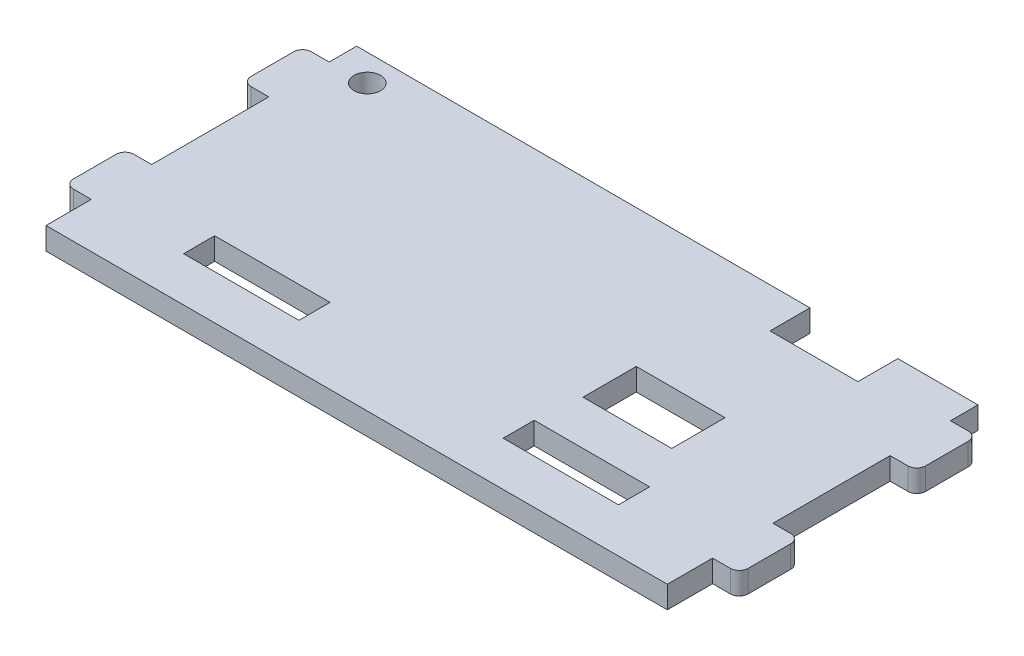
SolidWorks part; units mm, degrees
ref_plane "前视" through (0, 0, 0) normal (0, 0, 1) x (1, 0, 0)
ref_plane "上视" through (0, 0, 0) normal (0, 1, 0) x (1, 0, 0)
ref_plane "右视" through (0, 0, 0) normal (1, 0, 0) x (0, 0, -1)
sketch "草图1" plane through (0, 0, 0) normal (0, 1, 0) x (1, 0, 0)
  line L1 (-38, 17.5) -> (38, 17.5)
  line L2 (-38, 17.5) -> (-38, -17.5)
  line L3 (-38, -17.5) -> (38, -17.5)
  line L4 (38, 17.5) -> (38, -17.5)
  line L5 (-38, 17.5) -> (38, -17.5) construction
  line L6 (-38, -17.5) -> (38, 17.5) construction
  point P0 (0, 0)
  dimension "D1" = 35
  dimension "D2" = 76
extrude "凸台-拉伸1" add sketch "草图1" along normal blind 2.5
sketch "草图2" plane through (0, 2.5, 0) normal (0, 1, 0) x (1, 0, 0)
  line L0 (-38, -17.5) -> (38, -17.5) construction
  line L1 (-24.5, -9) -> (-11.5, -9)
  line L2 (-24.5, -9) -> (-24.5, -12.5)
  line L3 (-24.5, -12.5) -> (-11.5, -12.5)
  line L4 (-11.5, -9) -> (-11.5, -12.5)
  line L5 (-24.5, -9) -> (-11.5, -12.5) construction
  line L6 (-24.5, -12.5) -> (-11.5, -9) construction
  line L7 (-38, 17.5) -> (-38, -17.5) construction
  line L8 (0, 0) -> (0, -2.6782) construction
  line L9 (24.5, -12.5) -> (11.5, -12.5)
  line L10 (11.5, -9) -> (11.5, -12.5)
  line L11 (24.5, -9) -> (11.5, -9)
  line L12 (24.5, -9) -> (24.5, -12.5)
  point P0 (-18, -10.75)
  dimension "D1" = 5
  dimension "D2" = 13.5
  dimension "D3" = 13
  dimension "D4" = 3.5
extrude "切除-拉伸1" cut sketch "草图2" against normal through all
sketch "草图3" plane through (0, 2.5, 0) normal (0, 1, 0) x (1, 0, 0)
  line L0 (-38, -17.5) -> (-35, -17.5)
  line L1 (-38, -17.5) -> (38, -17.5) construction
  line L2 (-35, -17.5) -> (-35, -12.4)
  line L3 (-35, -12.4) -> (-38, -12.4)
  line L4 (-38, 17.5) -> (-38, -17.5) construction
  line L5 (-38, -12.4) -> (-38, -17.5)
  line L6 (-38, 17.5) -> (-35, 17.5)
  line L7 (38, 17.5) -> (-38, 17.5) construction
  line L8 (-35, 17.5) -> (-35, 14.4)
  line L9 (-35, 14.4) -> (-38, 14.4)
  line L10 (-38, 14.4) -> (-38, 17.5)
  line L11 (-38, 7.6) -> (-35, 7.6)
  line L12 (-35, 7.6) -> (-35, -5.6)
  line L13 (-35, -5.6) -> (-38, -5.6)
  line L14 (-38, -5.6) -> (-38, 7.6)
  line L15 (0, 0) -> (0, 5.419) construction
  line L16 (38, -17.5) -> (35, -17.5)
  line L17 (38, -12.4) -> (38, -17.5)
  line L18 (35, -17.5) -> (35, -12.4)
  line L19 (35, -12.4) -> (38, -12.4)
  line L20 (35, -5.6) -> (38, -5.6)
  line L21 (38, -5.6) -> (38, 7.6)
  line L22 (35, 7.6) -> (35, -5.6)
  line L23 (38, 7.6) -> (35, 7.6)
  line L24 (35, 14.4) -> (38, 14.4)
  line L25 (35, 17.5) -> (35, 14.4)
  line L26 (38, 17.5) -> (35, 17.5)
  line L27 (38, 14.4) -> (38, 17.5)
  dimension "D1" = 3
  dimension "D2" = 5.1
  dimension "D3" = 3
  dimension "D4" = 3.1
  dimension "D5" = 3
  dimension "D6" = 6.8
  dimension "D7" = 6.8
extrude "切除-拉伸2" cut sketch "草图3" against normal through all
fillet "圆角1" radius 1 8 edges at (38, 1.25, -14.4) (38, 1.25, -7.6) (38, 1.25, 5.6) (38, 1.25, 12.4) (-38, 1.25, 12.4) (-38, 1.25, 5.6) (-38, 1.25, -7.6) (-38, 1.25, -14.4)
sketch "草图4" plane through (0, 2.5, 0) normal (0, 1, 0) x (1, 0, 0)
  line L0 (35, 17.5) -> (-35, 17.5) construction
  line L1 (35, 17.5) -> (35, 14.4) construction
  line L2 (-35, 14.4) -> (-35, 17.5) construction
  line L3 (18.0812, 14.5) -> (26.9965, 14.5) construction
  line L4 (25.9681, 17.5) -> (25.9681, 13)
  line L5 (25.9681, 13) -> (16.0681, 13)
  line L6 (16.0681, 13) -> (16.0681, 17.5)
  line L7 (16.0681, 17.5) -> (25.9681, 17.5)
  circle A0 centre (-30.8, 14.5) radius 1.5
  point P4 (-35, 15.95)
  dimension "D1" = 3
  dimension "D2" = 4.2
  dimension "D3" = 4.5
  dimension "D4" = 9.9
  dimension "D5" = 9.0319
extrude "切除-拉伸3" cut sketch "草图4" against normal through all
sketch "草图5" plane through (0, 2.5, 0) normal (0, 1, 0) x (1, 0, 0)
  line L0 (35, 7.6) -> (35, -5.6) construction
  line L1 (12, 2) -> (22, 2)
  line L2 (12, 2) -> (12, -4)
  line L3 (12, -4) -> (22, -4)
  line L4 (22, 2) -> (22, -4)
  line L5 (12, 2) -> (22, -4) construction
  line L6 (12, -4) -> (22, 2) construction
  line L7 (24.5, -9) -> (11.5, -9) construction
  point P0 (17, -1)
  dimension "D1" = 10
  dimension "D2" = 6
  dimension "D3" = 18
  dimension "D4" = 8
extrude "切除-拉伸4" cut sketch "草图5" against normal through all
